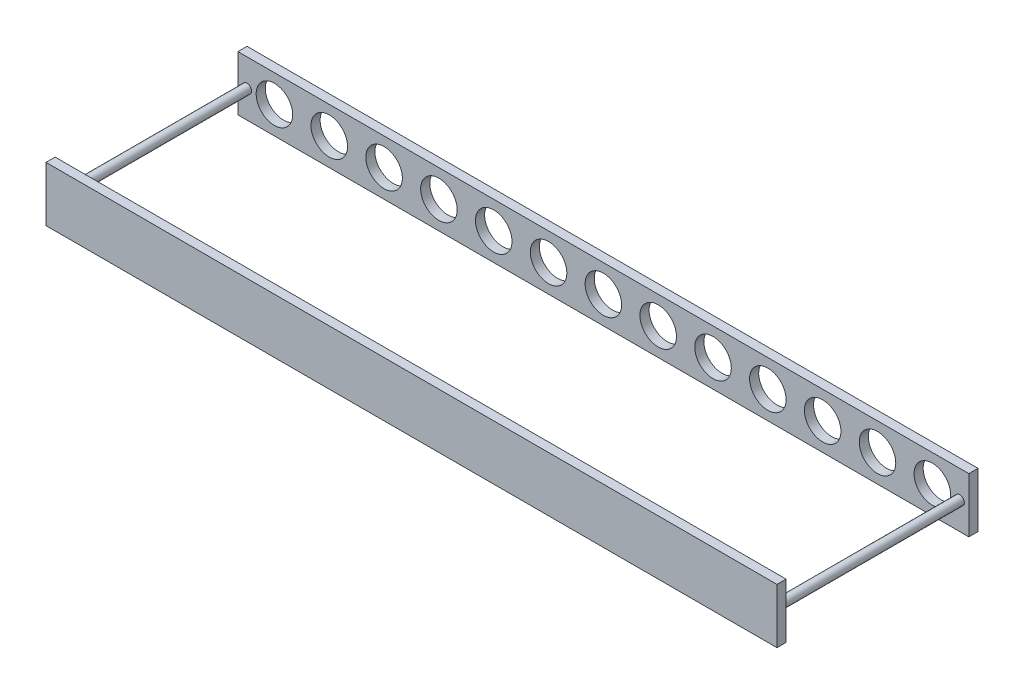
SolidWorks part; units mm, degrees
ref_plane "Front Plane" through (0, 0, 0) normal (0, 0, 1) x (1, 0, 0)
ref_plane "Top Plane" through (0, 0, 0) normal (0, 1, 0) x (1, 0, 0)
ref_plane "Right Plane" through (0, 0, 0) normal (1, 0, 0) x (0, 0, -1)
sketch "Sketch1" plane through (0, 0, 0) normal (0, 0, 1) x (1, 0, 0)
  line L1 (-400, 30) -> (400, 30)
  line L2 (-400, 30) -> (-400, -30)
  line L3 (-400, -30) -> (400, -30)
  line L4 (400, 30) -> (400, -30)
  line L5 (-400, 30) -> (400, -30) construction
  line L6 (-400, -30) -> (400, 30) construction
  point P0 (0, 0)
  dimension "D1" = 60
  dimension "D2" = 800
extrude "Boss-Extrude1" add sketch "Sketch1" along normal blind 10
sketch "Sketch2" plane through (0, 0, 0) normal (0, 0, 1) x (1, 0, 0)
  circle A0 centre (0, 0) radius 20
extrude "Cut-Extrude6" cut sketch "Sketch2" along normal blind 10
pattern_linear "LPattern1" count 7 spacing 60 along (1, 0, 0) of "Cut-Extrude6"
pattern_linear "LPattern2" count 7 spacing 60 along (-1, 0, 0) of "LPattern1"
sketch "Sketch3" plane through (0, 0, 10) normal (0, 0, 1) x (1, 0, 0)
  circle A0 centre (-390, 0) radius 5
  circle A1 centre (390, 0) radius 5
extrude "Boss-Extrude2" add sketch "Sketch3" along normal blind 200
sketch "Sketch4" plane through (0, 0, 210) normal (0, 0, 1) x (1, 0, 0)
  line L1 (400, 30) -> (-400, 30)
  line L2 (400, 30) -> (400, -30)
  line L3 (400, -30) -> (-400, -30)
  line L4 (-400, 30) -> (-400, -30)
  line L5 (400, 30) -> (-400, -30) construction
  line L6 (400, -30) -> (-400, 30) construction
  point P0 (0, 0)
  dimension "D1" = 800
  dimension "D2" = 60
extrude "Boss-Extrude3" add sketch "Sketch4" along normal blind 10
